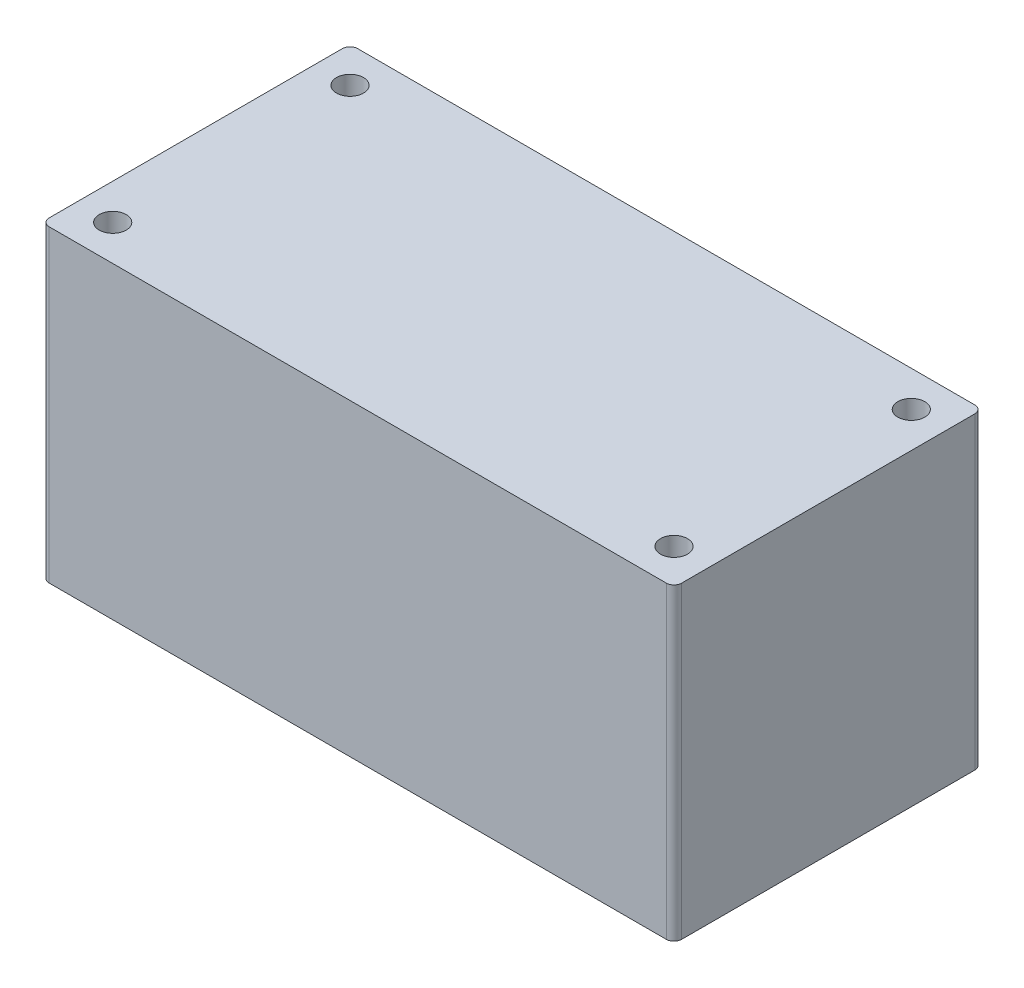
SolidWorks part; units mm, degrees
material "Custom Plastic"
ref_plane "Front Plane" through (0, 0, 0) normal (0, 0, 1) x (1, 0, 0)
ref_plane "Top Plane" through (0, 0, 0) normal (0, 1, 0) x (1, 0, 0)
ref_plane "Right Plane" through (0, 0, 0) normal (1, 0, 0) x (0, 0, -1)
sketch "Sketch2" plane through (0, 0, 0) normal (0, 1, 0) x (1, 0, 0)
  line L1 (-20.5, -10) -> (20.5, -10)
  line L2 (-20.5, -10) -> (-20.5, 10)
  line L3 (-20.5, 10) -> (20.5, 10)
  line L4 (20.5, -10) -> (20.5, 10)
  line L5 (-20.5, -10) -> (20.5, 10) construction
  line L6 (-20.5, 10) -> (20.5, -10) construction
  point P0 (0, 0)
extrude "Boss-Extrude1" add sketch "Sketch2" along normal blind 20
fillet "Fillet1" radius 0.5 4 edges at (-20.5, 10, -10) (20.5, 10, -10) (20.5, 10, 10) (-20.5, 10, 10)
sketch "Sketch3" plane through (0, 20, 0) normal (0, 1, 0) x (1, 0, 0)
  circle A0 centre (18.1909, 7.6909) radius 0.875 construction
  circle A1 centre (18.1909, -7.6909) radius 0.875 construction
  circle A2 centre (-18.1909, 7.6909) radius 0.875 construction
  circle A3 centre (-18.1909, -7.6909) radius 0.875 construction
  circle A4 centre (18.1909, 7.6909) radius 0.875
  circle A5 centre (18.1909, -7.6909) radius 0.875
  circle A6 centre (-18.1909, 7.6909) radius 0.875
  circle A7 centre (-18.1909, -7.6909) radius 0.875
extrude "Cut-Extrude1" cut sketch "Sketch3" against normal through all
